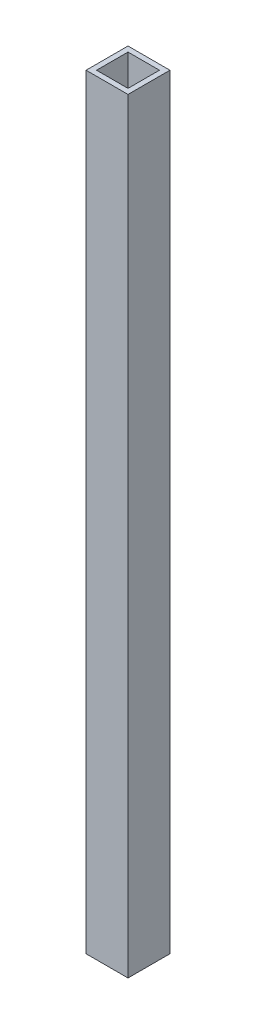
SolidWorks part; units mm, degrees
material "Plain Carbon Steel"
ref_plane "Front Plane" through (0, 0, 0) normal (0, 0, 1) x (1, 0, 0)
ref_plane "Top Plane" through (0, 0, 0) normal (0, 1, 0) x (1, 0, 0)
ref_plane "Right Plane" through (0, 0, 0) normal (1, 0, 0) x (0, 0, -1)
sketch "Sketch1" plane through (0, 0, 0) normal (0, 1, 0) x (1, 0, 0)
  line L1 (-25.4, -25.4) -> (25.4, -25.4)
  line L2 (-25.4, -25.4) -> (-25.4, 25.4)
  line L3 (-25.4, 25.4) -> (25.4, 25.4)
  line L4 (25.4, -25.4) -> (25.4, 25.4)
  line L5 (-25.4, -25.4) -> (25.4, 25.4) construction
  line L6 (-25.4, 25.4) -> (25.4, -25.4) construction
  line L7 (-19.05, -19.05) -> (19.05, -19.05)
  line L8 (-19.05, -19.05) -> (-19.05, 19.05)
  line L9 (-19.05, 19.05) -> (19.05, 19.05)
  line L10 (19.05, -19.05) -> (19.05, 19.05)
  line L11 (-19.05, -19.05) -> (19.05, 19.05) construction
  line L12 (-19.05, 19.05) -> (19.05, -19.05) construction
  point P0 (0, 0)
  point P6 (0, 0)
  dimension "D1" = 6.35
  dimension "D2" = 6.35
  dimension "D3" = 50.8
extrude "Boss-Extrude1" add sketch "Sketch1" along normal mid plane 927.1
equation "\"D2@Sketch1\" = \"D1@Sketch1\""
